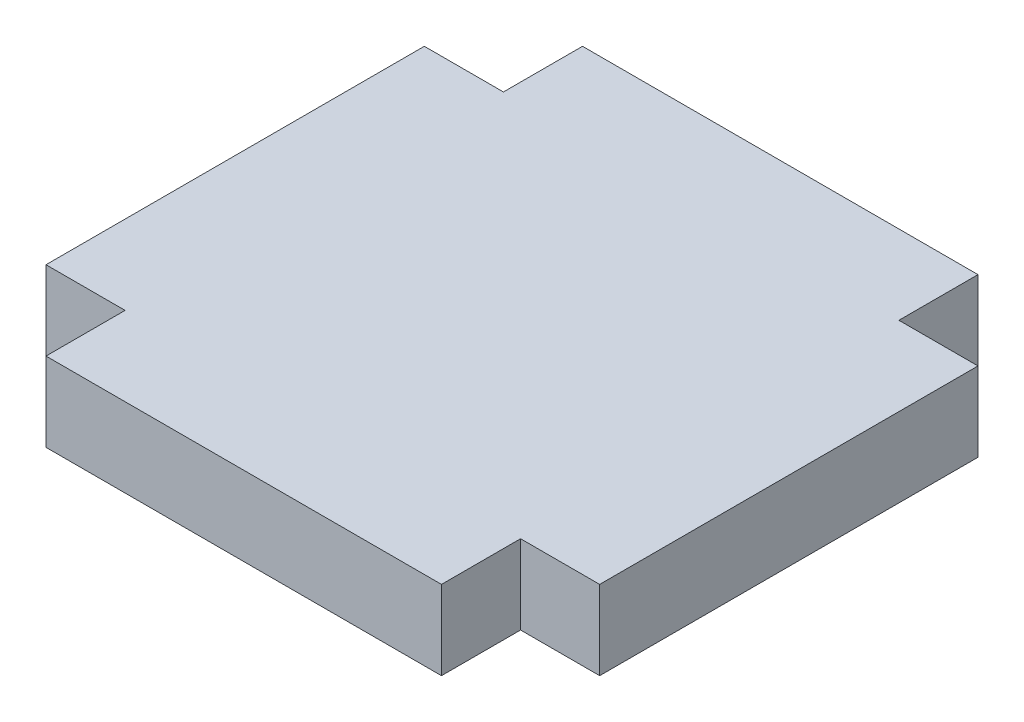
SolidWorks part; units mm, degrees
ref_plane "Front Plane" through (0, 0, 0) normal (0, 0, 1) x (1, 0, 0)
ref_plane "Top Plane" through (0, 0, 0) normal (0, 1, 0) x (1, 0, 0)
ref_plane "Right Plane" through (0, 0, 0) normal (1, 0, 0) x (0, 0, -1)
sketch "Sketch1" plane through (0, 0, 0) normal (0, 1, 0) x (1, 0, 0)
  line L0 (-7.5, 10.175) -> (7.5, 10.175)
  line L1 (7.5, 10.175) -> (7.5, 7.175)
  line L2 (7.5, 7.175) -> (10.5, 7.175)
  line L3 (10.5, 7.175) -> (10.5, -7.175)
  line L4 (10.5, -7.175) -> (7.5, -7.175)
  line L5 (7.5, -7.175) -> (7.5, -10.175)
  line L6 (7.5, -10.175) -> (-7.5, -10.175)
  line L7 (-7.5, -10.175) -> (-7.5, -7.175)
  line L8 (-7.5, -7.175) -> (-10.5, -7.175)
  line L9 (-10.5, -7.175) -> (-10.5, 7.175)
  line L10 (-10.5, 7.175) -> (-7.5, 7.175)
  line L11 (-7.5, 7.175) -> (-7.5, 10.175)
  point P2 (0, 10.175)
  point P13 (10.5, 0)
  dimension "D1" = 15
  dimension "D2" = 3
  dimension "D3" = 3
  dimension "D4" = 14.35
extrude "Boss-Extrude1" add sketch "Sketch1" along normal mid plane 3
